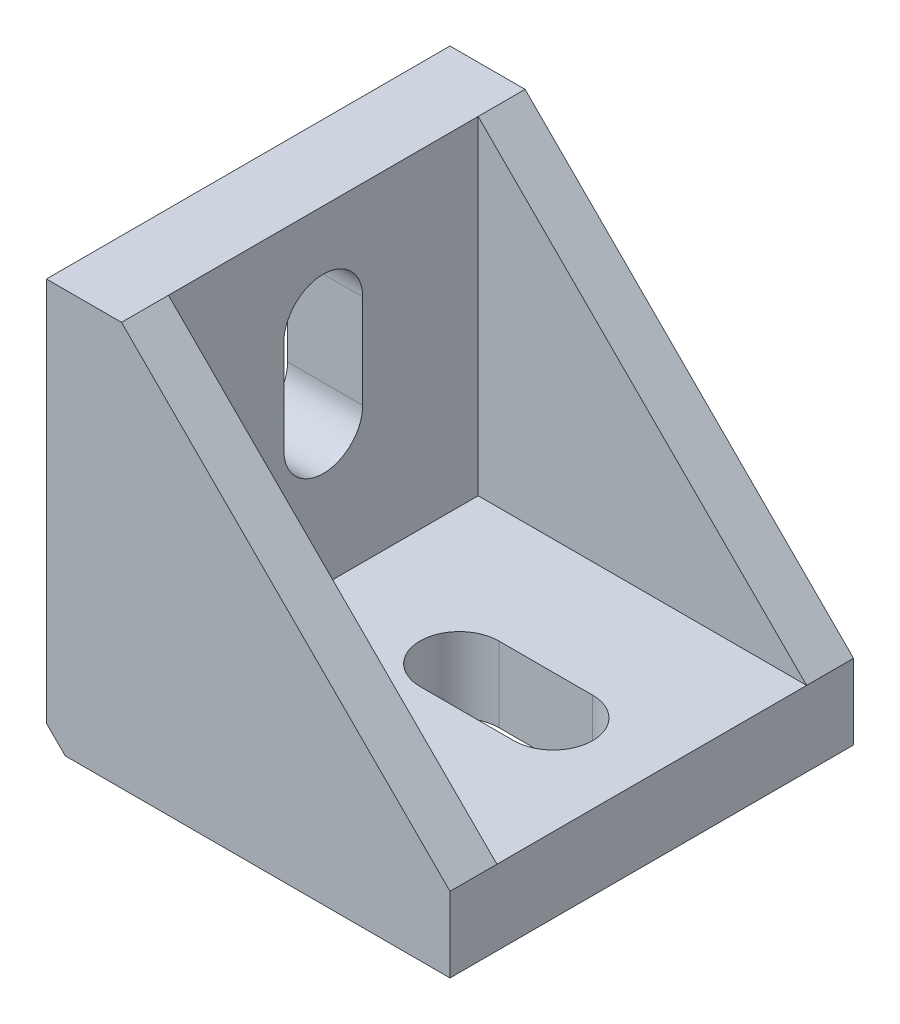
SolidWorks part; units mm, degrees
material "Alumina"
ref_plane "Front Plane" through (0, 0, 0) normal (0, 0, 1) x (1, 0, 0)
ref_plane "Top Plane" through (0, 0, 0) normal (0, 1, 0) x (1, 0, 0)
ref_plane "Right Plane" through (0, 0, 0) normal (1, 0, 0) x (0, 0, -1)
sketch "Esquisse1" plane through (0, 0, 0) normal (0, 0, 1) x (1, 0, 0)
  line L0 (0, 43) -> (0, 0)
  line L1 (0, 0) -> (43, 0)
  line L2 (43, 0) -> (43, 8)
  line L3 (43, 8) -> (8, 43)
  line L4 (8, 43) -> (0, 43)
  dimension "D1" = 43
  dimension "D2" = 43
  dimension "D3" = 8
  dimension "D4" = 8
extrude "Boss.-Extru.1" add sketch "Esquisse1" along normal blind 43
ref_plane "Plan1" through (0, 0, 21.5) normal (0, 0, 1) x (1, 0, 0)
sketch "Esquisse2" plane through (0, 0, 21.5) normal (0, 0, 1) x (1, 0, 0)
  line L0 (8, 43.5588) -> (8, 8)
  line L1 (8, 8) -> (47.7749, 8)
  line L2 (47.7749, 8) -> (49.4278, 41.5156)
  line L3 (49.4278, 41.5156) -> (8, 43.5588)
  line L6 (0, 43) -> (0, 0) construction
  line L7 (0, 0) -> (43, 0) construction
  dimension "D1" = 8
  dimension "D2" = 8
extrude "Enlèv. mat.-Extru.1" cut sketch "Esquisse2" against normal mid plane 33
sketch "Esquisse3" plane through (8, 0, 0) normal (1, 0, 0) x (0, 0, -1)
  line L5 (-21.5, 22.5) -> (-21.5, 32.5) construction
  line L7 (-25.7, 22.5) -> (-25.7, 32.5)
  line L8 (-17.3, 22.5) -> (-17.3, 32.5)
  line L9 (-5, 43) -> (-5, 8) construction
  line L10 (-38, 43) -> (-38, 8) construction
  line L11 (-43, 0) -> (0, 0) construction
  arc A1 (-25.7, 22.5) -> (-17.3, 22.5) centre (-21.5, 22.5) ccw
  arc A2 (-17.3, 32.5) -> (-25.7, 32.5) centre (-21.5, 32.5) ccw
  point P2 (-21.5, 27.5)
  dimension "D1" = 4.2
  dimension "D2" = 10
  dimension "D3" = 22.5
extrude "Enlèv. mat.-Extru.2" cut sketch "Esquisse3" along normal through all both and the other way through all
sketch "Esquisse4" plane through (0, 8, 0) normal (0, 1, 0) x (1, 0, 0)
  line L0 (8, -5) -> (43, -5) construction
  line L6 (32.5, -21.5) -> (22.5, -21.5) construction
  line L7 (32.5, -25.7) -> (22.5, -25.7)
  line L8 (32.5, -17.3) -> (22.5, -17.3)
  line L9 (8, -38) -> (43, -38) construction
  line L10 (0, -43) -> (0, 0) construction
  arc A0 (32.5, -25.7) -> (32.5, -17.3) centre (32.5, -21.5) ccw
  arc A1 (22.5, -17.3) -> (22.5, -25.7) centre (22.5, -21.5) ccw
  point P2 (27.5, -21.5)
  dimension "D1" = 4.2
  dimension "D2" = 10
  dimension "D3" = 22.5
extrude "Enlèv. mat.-Extru.3" cut sketch "Esquisse4" against normal through all
chamfer "Chanfrein1" distance 2 angle 45 1 edges at (0, 0, 21.5)
